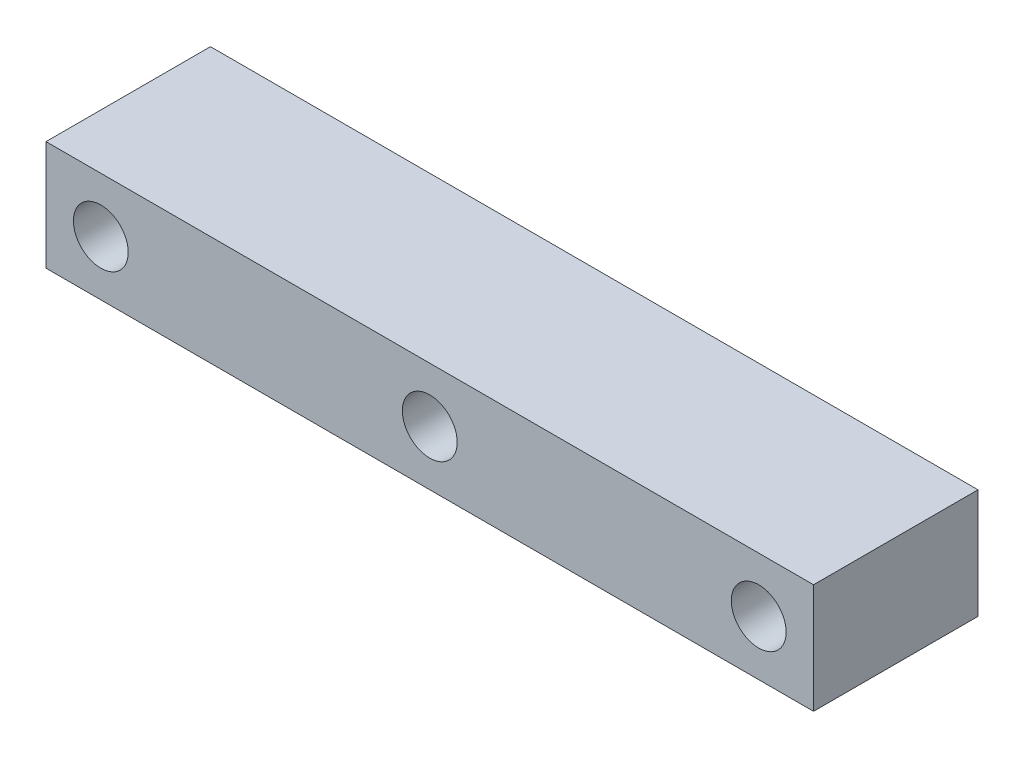
SolidWorks part; units mm, degrees
material "6061-T6 (SS)"
ref_plane "Front Plane" through (0, 0, 0) normal (0, 0, 1) x (1, 0, 0)
ref_plane "Top Plane" through (0, 0, 0) normal (0, 1, 0) x (1, 0, 0)
ref_plane "Right Plane" through (0, 0, 0) normal (1, 0, 0) x (0, 0, -1)
sketch "Sketch1" plane through (0, 0, 0) normal (0, 0, 1) x (1, 0, 0)
  line L1 (-88.9, 12.7) -> (88.9, 12.7)
  line L2 (-88.9, 12.7) -> (-88.9, -12.7)
  line L3 (-88.9, -12.7) -> (88.9, -12.7)
  line L4 (88.9, 12.7) -> (88.9, -12.7)
  circle A0 centre (-76.2, 0) radius 6.35
  circle A1 centre (0, 0) radius 6.35
  circle A2 centre (76.2, 0) radius 6.35
  point P4 (-76.2, 12.7)
  point P5 (76.2, 12.7)
  point P6 (0, 12.7)
  point P8 (-88.9, 0)
  dimension "D5" = 12.7
  dimension "D1" = 25.4
  dimension "D2" = 177.8
  dimension "D3" = 76.2
  dimension "D4" = 76.2
extrude "Boss-Extrude1" add sketch "Sketch1" along normal blind 38.1
